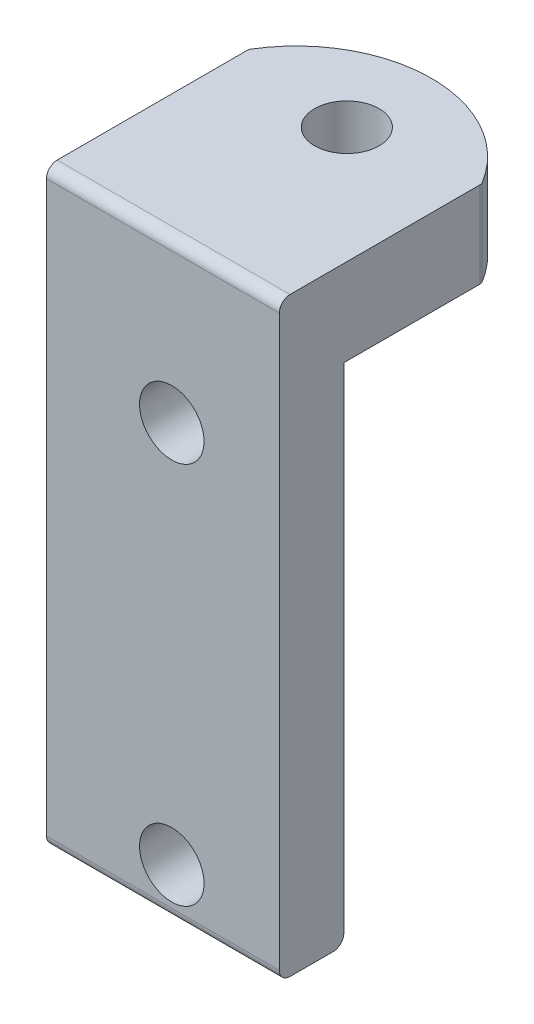
SolidWorks part; units mm, degrees
ref_plane "Plano frontal" through (0, 0, 0) normal (0, 0, 1) x (1, 0, 0)
ref_plane "Plano superior" through (0, 0, 0) normal (0, 1, 0) x (1, 0, 0)
ref_plane "Plano direito" through (0, 0, 0) normal (1, 0, 0) x (0, 0, -1)
sketch "Esboço2" plane through (0, 0, 0) normal (0, 0, 1) x (1, 0, 0)
  line L8 (18.6731, 27.4559) -> (18.6731, 15.0942)
  line L9 (18.6731, 33.5933) -> (7.8449, 33.5933)
  line L11 (18.6731, 10.1251) -> (7.8449, 10.1251)
  line L12 (7.8449, 33.5933) -> (7.8449, 10.1251)
  line L24 (18.6731, 10.1251) -> (18.6731, 15.0942)
  line L28 (18.6731, 27.4559) -> (18.6731, 33.5933)
  circle A2 centre (13.6731, 30.1751) radius 1.5
  circle A3 centre (13.6731, 12.3751) radius 1.5
extrude "Ressalto-extrusão1" add sketch "Esboço2" along normal blind 3
sketch "Esboço3" plane through (0, 33.5933, 0) normal (0, 1, 0) x (1, 0, 0)
  line L4 (18.6731, 0) -> (7.8449, 0)
  line L5 (7.8449, 0) -> (7.8449, -3)
  line L6 (7.8449, -3) -> (18.6731, -3)
  line L7 (18.6731, -3) -> (18.6731, 0)
  line L9 (7.8449, 0) -> (7.8449, -3)
  line L10 (7.8449, -3) -> (18.6731, -3)
  line L11 (18.6731, -3) -> (18.6731, 0)
  circle A1 centre (13.259, 5.5546) radius 1.5
  arc A2 (7.8449, 0) -> (18.6731, 0) centre (13.259, 3.2042) cw
  dimension "D1" = 0
  dimension "D3" = 3
extrude "Ressalto-extrusão2" add sketch "Esboço3" along normal blind 4
sketch "Esboço4" plane through (0, 0, 0) normal (0, 1, 0) x (1, 0, 0)
  line L0 (7.8449, 0) -> (7.8449, 6.4085)
  line L1 (18.6731, 0) -> (18.6731, 6.4085)
  arc A0 (18.6731, 0) -> (7.8449, 0) centre (13.259, 3.2042) ccw construction
  arc A1 (7.8449, 0) -> (7.8449, 6.4085) centre (13.259, 3.2042) cw
  arc A2 (18.6731, 0) -> (18.6731, 6.4085) centre (13.259, 3.2042) ccw
extrude "Corte-extrusão1" cut sketch "Esboço4" along normal blind 800
fillet "Filete3" radius 0.5 1 edges at (13.259, 37.5933, 3)
fillet "Filete4" radius 0.25 1 edges at (18.6731, 35.5933, -6.4085)
fillet "Filete5" radius 0.25 1 edges at (7.8449, 35.5933, -6.4085)
fillet "Filete6" radius 0.5 2 edges at (13.259, 10.1251, 0) (13.259, 10.1251, 3)
